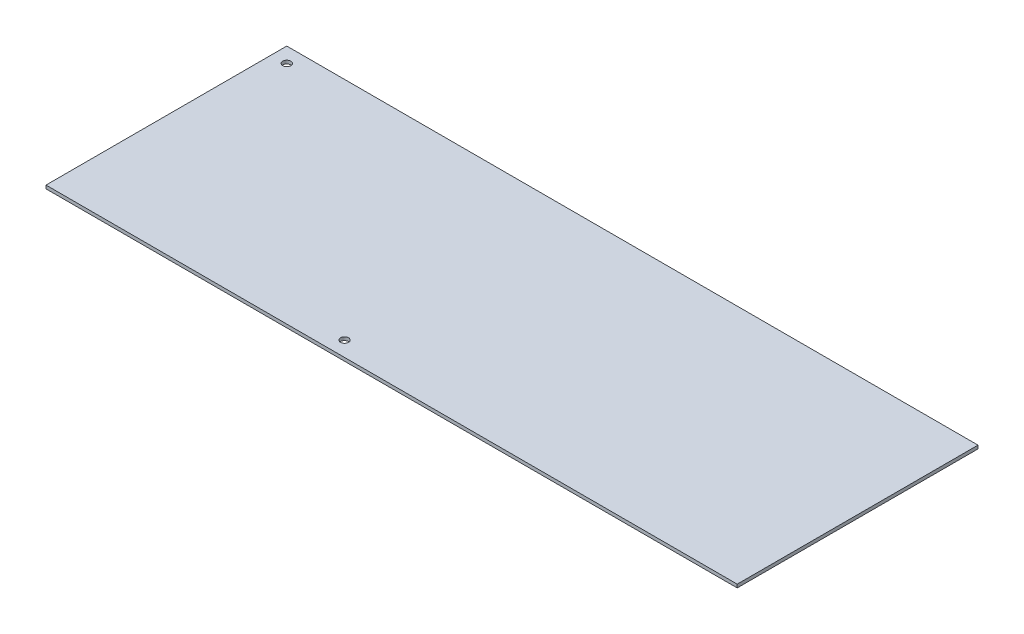
SolidWorks part; units mm, degrees
material "Copper"
ref_plane "Front Plane" through (0, 0, 0) normal (0, 0, 1) x (1, 0, 0)
ref_plane "Top Plane" through (0, 0, 0) normal (0, 1, 0) x (1, 0, 0)
ref_plane "Right Plane" through (0, 0, 0) normal (1, 0, 0) x (0, 0, -1)
sketch "Sketch1" plane through (0, 0, 0) normal (0, 1, 0) x (1, 0, 0)
  line L1 (0, 0) -> (344.4875, 0)
  line L2 (0, 0) -> (0, 120)
  line L3 (0, 120) -> (344.4875, 120)
  line L4 (344.4875, 0) -> (344.4875, 120)
  circle A0 centre (141.2875, 7.5) radius 2
  point P5 (141.2875, 7.5)
extrude "Boss-Extrude1" add sketch "Sketch1" along normal blind 1.65
sketch "Sketch2" plane through (0, 1.65, 0) normal (0, 1, 0) x (1, 0, 0)
  circle A0 centre (7.5, 112.5) radius 2
  point P7 (7.5, 112.5)
extrude "Cut-Extrude1" cut sketch "Sketch2" against normal blind 10
